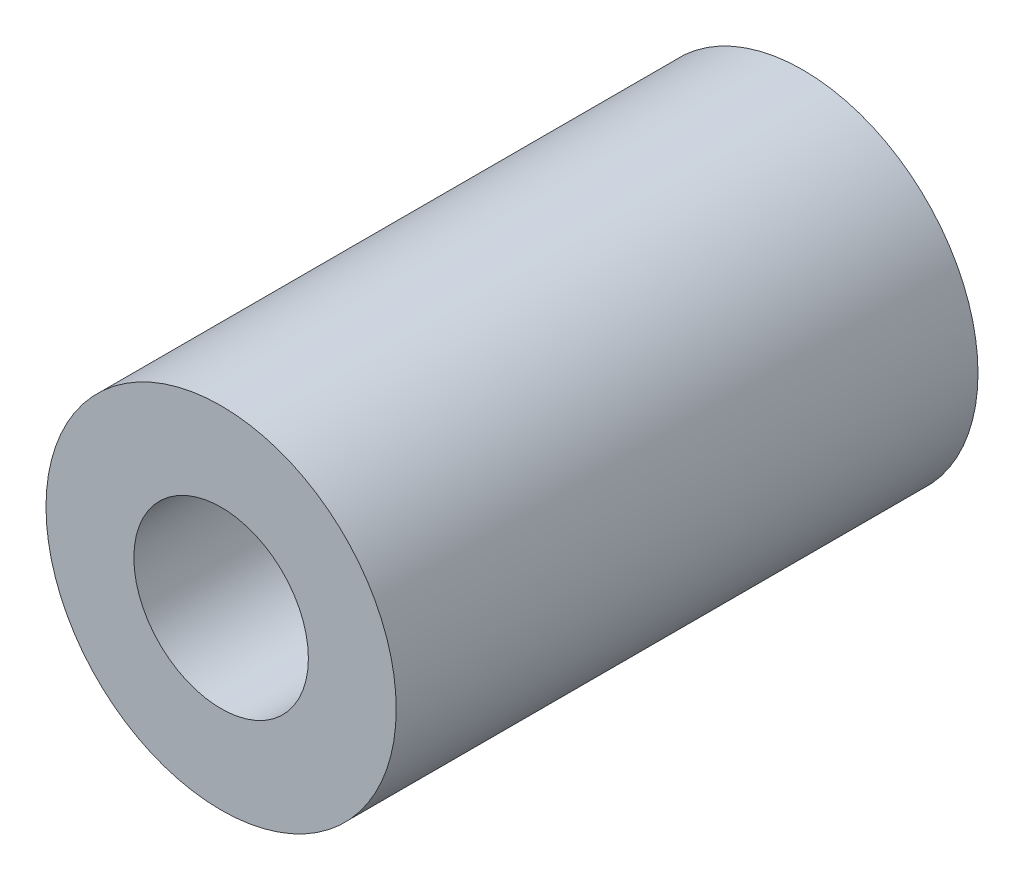
SolidWorks part; units mm, degrees
ref_plane "Front Plane" through (0, 0, 0) normal (0, 0, 1) x (1, 0, 0)
ref_plane "Top Plane" through (0, 0, 0) normal (0, 1, 0) x (1, 0, 0)
ref_plane "Right Plane" through (0, 0, 0) normal (1, 0, 0) x (0, 0, -1)
sketch "Sketch1" plane through (0, 0, 0) normal (0, 0, 1) x (1, 0, 0)
  circle A0 centre (0, 0) radius 3.01
  circle A1 centre (0, 0) radius 1.5
  dimension "D1" = 6.02
  dimension "ID" = 3
extrude "Extrude1" add sketch "Sketch1" along normal mid plane 10
sketch "Sketch2" plane through (0, 0, 0) normal (1, 0, 0) x (0, 0, -1)
  line L0 (-5, -1.5) -> (5, -1.5) construction
  line L3 (5, 1.5) -> (-5, 1.5) construction
  line L5 (-5, -1.5) -> (5, -1.5)
  line L6 (5, 1.5) -> (-5, 1.5)
sketch "Sketch4" plane through (0, 0, 5) normal (0, 0, 1) x (1, 0, 0)
  line L0 (0, 0) -> (-1.0607, 1.0607)
  line L1 (0, -3.3) -> (0, 3.3) construction
  circle A0 centre (0, 0) radius 1.5 construction
  dimension "D1" = 45
